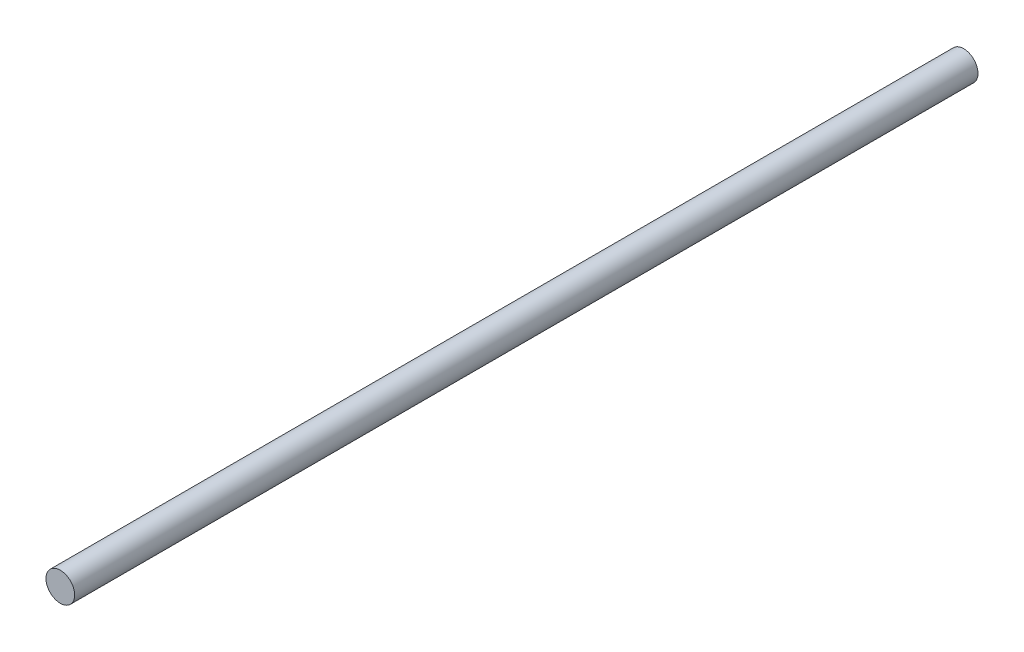
SolidWorks part; units mm, degrees
ref_plane "Front Plane" through (0, 0, 0) normal (0, 0, 1) x (1, 0, 0)
ref_plane "Top Plane" through (0, 0, 0) normal (0, 1, 0) x (1, 0, 0)
ref_plane "Right Plane" through (0, 0, 0) normal (1, 0, 0) x (0, 0, -1)
sketch "Sketch1" plane through (0, 0, 0) normal (0, 0, 1) x (1, 0, 0)
  circle A0 centre (0, 0) radius 1.5875
  dimension "D1" = 3.175
extrude "Boss-Extrude1" add sketch "Sketch1" along normal blind 100 contours A0
